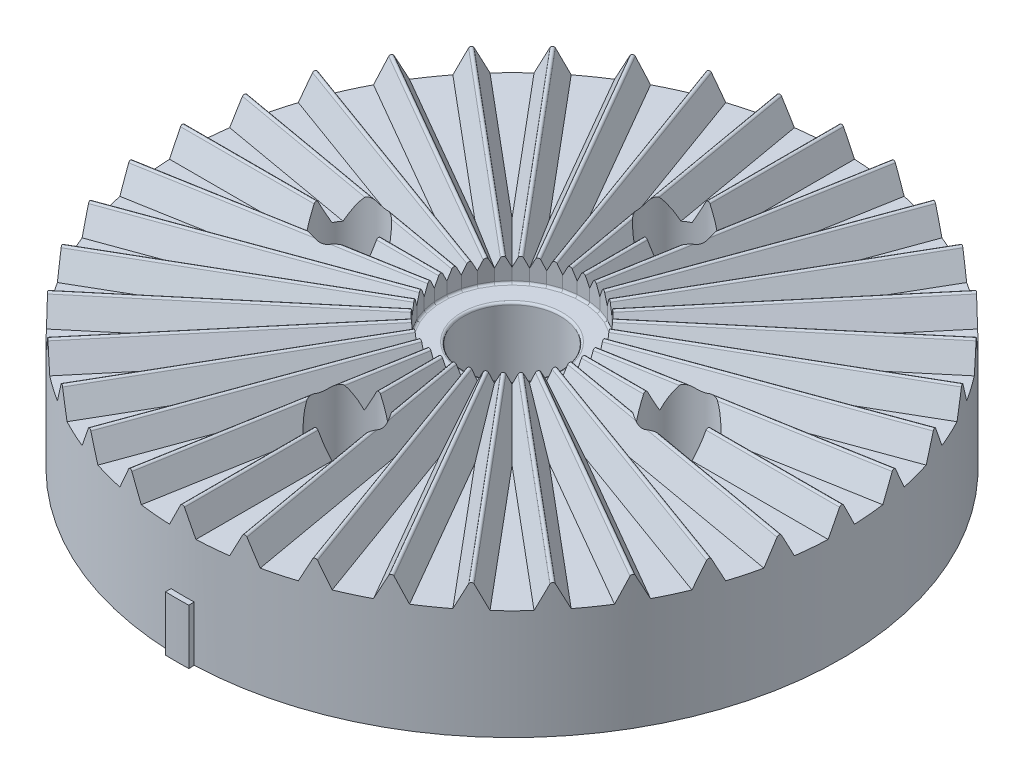
SolidWorks part; units mm, degrees
ref_plane "Front Plane" through (0, 0, 0) normal (0, 0, 1) x (1, 0, 0)
ref_plane "Top Plane" through (0, 0, 0) normal (0, 1, 0) x (1, 0, 0)
ref_plane "Right Plane" through (0, 0, 0) normal (1, 0, 0) x (0, 0, -1)
sketch "Axis of Rotation" plane through (0, 0, 0) normal (1, 0, 0) x (0, 0, -1)
  line L0 (0, 0) -> (0, 25.3147) construction
sketch "Sketch1" plane through (0, 0, 0) normal (0, 1, 0) x (1, 0, 0)
  circle A0 centre (0, 0) radius 30
  dimension "D1" = 60
extrude "Body" add sketch "Sketch1" along normal blind 10
ref_plane "Cutting Plane" through (30, 0, 0) normal (1, 0, 0) x (0, 0, -1)
sketch "Sketch4" plane through (0, 0, 0) normal (0, 1, 0) x (1, 0, 0)
  circle A0 centre (0, 0) radius 4.4
  dimension "D1" = 8.8
extrude "Center Hole" cut sketch "Sketch4" along normal through all
sketch "Sketch3" plane through (30, 0, 0) normal (1, 0, 0) x (0, 0, -1)
  line L0 (-1.2, 10) -> (-0.1789, 12.0422)
  line L1 (30, 10) -> (-30, 10) construction
  line L3 (0.1789, 12.0422) -> (1.2, 10)
  line L4 (1.2, 10) -> (-1.2, 10)
  line L5 (0, 20.5746) -> (0, 12.1009) construction
  arc A0 (0.1789, 12.0422) -> (-0.1789, 12.0422) centre (0, 11.9528) ccw
  point P16 (0, 12.4)
  dimension "D3" = 0.2
  dimension "D2" = 2.4
  dimension "D1" = 2.4
extrude "Rail" add sketch "Sketch3" against normal blind 23.5
pattern_circular "Rail Pattern" count 36 over 360 about axis through (0, 0, 0) along (0, 1, 0) of "Rail"
sketch "Sketch9" plane through (0, 0, 0) normal (0, 0, 1) x (1, 0, 0)
  line L0 (30, 0) -> (30, 10) construction
  line L1 (30, 20) -> (32, 20)
  line L2 (30, 20) -> (30, 0)
  line L3 (30, 0) -> (32, 0)
  line L4 (32, 20) -> (32, 0)
  line L5 (30, 20) -> (32, 0) construction
  line L6 (30, 0) -> (32, 20) construction
  line L7 (-30, 0) -> (30, 0) construction
  point P4 (31, 10)
  dimension "D1" = 20
  dimension "D2" = 2
revolve "Rail Trim" cut sketch "Sketch9" angle 360 about L0
sketch "Sketch5" plane through (0, 0, 0) normal (1, 0, 0) x (0, 0, -1)
  line L0 (-30, 12.1527) -> (-30, 0) construction
  line L1 (-30.5, 5) -> (-30, 5)
  line L2 (-30.5, 5) -> (-30.5, 0)
  line L3 (-30.5, 0) -> (-30, 0)
  line L4 (-30, 5) -> (-30, 0)
  line L5 (-30.5, 5) -> (-30, 0) construction
  line L6 (-30.5, 0) -> (-30, 5) construction
  line L7 (-30, 0) -> (30, 0) construction
  line L8 (-30, 10) -> (-30, 0) construction
  line L10 (30, 10) -> (-30, 10) construction
  line L11 (-30, 12.1527) -> (-30, 0) construction
  point P4 (-30.25, 2.5)
  dimension "D1" = 0.5
revolve "Angle Indicator" add sketch "Sketch5" angle 2 about L0 other way angle 2
ref_plane "Mounting Hole Cutting Plane" through (0, 10, 0) normal (0, 1, 0) x (1, 0, 0)
sketch "Sketch6" plane through (0, 10, 0) normal (0, 1, 0) x (1, 0, 0)
  circle A0 centre (0, 0) radius 15 construction
  circle A1 centre (0, -15) radius 1.6
  circle A2 centre (-15, 0) radius 1.6
  circle A3 centre (0, 15) radius 1.6
  circle A4 centre (15, 0) radius 1.6
  point P14 (0, 0)
  dimension "D1" = 30
  dimension "D2" = 3.2
  dimension "D3" = 4
extrude "Mounting Hole Pattern" cut sketch "Sketch6" against normal through all
sketch "Sketch7" plane through (0, 10, 0) normal (0, 1, 0) x (1, 0, 0)
  circle A0 centre (0, 0) radius 15 construction
  circle A1 centre (0, 15) radius 2.85
  circle A2 centre (15, 0) radius 2.85
  circle A3 centre (0, -15) radius 2.85
  circle A4 centre (-15, 0) radius 2.85
  point P14 (0, 0)
  dimension "D1" = 30
  dimension "D2" = 5.7
  dimension "D3" = 4
extrude "Mounting Hole Pattern Counterbore" cut sketch "Sketch7" against normal blind 6 and the other way through all
fillet "Shaft Fillet" radius 0.2 37 edges at (0, 10, 4.4) (6.5, 10, 0) (6.4013, 10, 1.1287) (6.108, 10, 2.2231) (5.6292, 10, 3.25) (4.9793, 10, 4.1781) (4.1781, 10, 4.9793) (3.25, 10, 5.6292) (2.2231, 10, 6.108) (1.1287, 10, 6.4013) (0, 10, 6.5) (-1.1287, 10, 6.4013) (-2.2231, 10, 6.108) (-3.25, 10, 5.6292) (-4.1781, 10, 4.9793) (-4.9793, 10, 4.1781) (-5.6292, 10, 3.25) (-6.108, 10, 2.2231) (-6.4013, 10, 1.1287) (-6.5, 10, 0) (-6.4013, 10, -1.1287) (-6.108, 10, -2.2231) (-5.6292, 10, -3.25) (-4.9793, 10, -4.1781) (-4.1781, 10, -4.9793) (-3.25, 10, -5.6292) (-2.2231, 10, -6.108) (-1.1287, 10, -6.4013) (0, 10, -6.5) (1.1287, 10, -6.4013) (2.2231, 10, -6.108) (3.25, 10, -5.6292) (4.1781, 10, -4.9793) (4.9793, 10, -4.1781) (5.6292, 10, -3.25) (6.108, 10, -2.2231) (6.4013, 10, -1.1287)
equation "\"OD\"= 60mm"
equation "\"D1@Sketch1\"=\"OD\""
equation "\"D1@Cutting Plane\" = \"OD\" / 2"
equation "\"num_rails\"= 36mm"
equation "\"rail_width\"= 2.4mm"
equation "\"rail_height\"= 2.4mm"
equation "\"ID\"= 8.8mm"
equation "\"D1@Sketch4\"=\"ID\""
equation "\"D2@Sketch3\"=\"rail_width\""
equation "\"Depth\"= 10mm"
equation "\"D1@Sketch3\"=\"rail_height\""
equation "\"D1@Rail Pattern\"=\"num_rails\""
equation "\"D1@Sketch9\"=\"Depth\" + 10"
